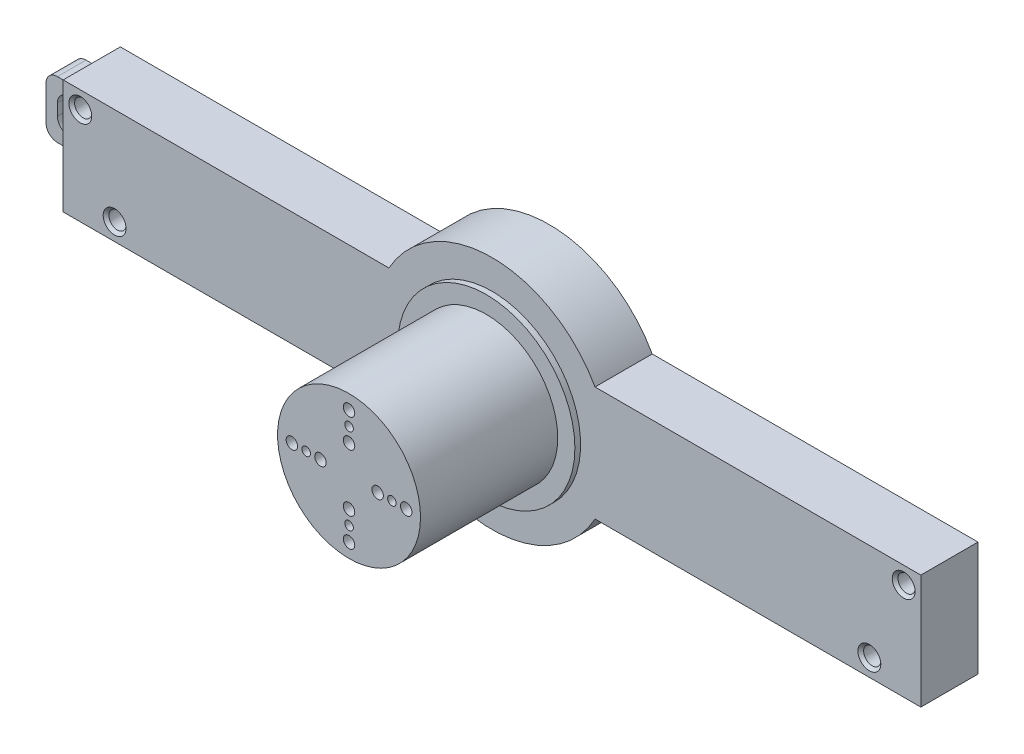
SolidWorks part; units mm, degrees
ref_plane "Płaszczyzna przednia" through (0, 0, 0) normal (0, 0, 1) x (1, 0, 0)
ref_plane "Płaszczyzna górna" through (0, 0, 0) normal (0, 1, 0) x (1, 0, 0)
ref_plane "Płaszczyzna prawa" through (0, 0, 0) normal (1, 0, 0) x (0, 0, -1)
sketch "Szkic1" plane through (0, 0, 0) normal (0, 0, 1) x (1, 0, 0)
  line L1 (-75, -10) -> (75, -10)
  line L2 (-75, -10) -> (-75, 10)
  line L3 (-75, 10) -> (75, 10)
  line L4 (75, -10) -> (75, 10)
  line L5 (-75, -10) -> (75, 10) construction
  line L6 (-75, 10) -> (75, -10) construction
  point P0 (0, 0)
  dimension "D1" = 150
  dimension "D2" = 20
extrude "Dodanie-wyciągnięcie1" add sketch "Szkic1" along normal blind 10
sketch "Szkic2" plane through (0, 0, 10) normal (0, 0, 1) x (1, 0, 0)
  circle A0 centre (0, 0) radius 20.6112
extrude "Dodanie-wyciągnięcie2" add sketch "Szkic2" against normal blind 10
sketch "Szkic3" plane through (0, 0, 10) normal (0, 0, 1) x (1, 0, 0)
  circle A0 centre (0, 0) radius 12.5
  dimension "D1" = 25
extrude "Dodanie-wyciągnięcie5" add sketch "Szkic3" along normal blind 25 contours A0
sketch "Szkic8" plane through (0, 0, 10) normal (0, 0, 1) x (1, 0, 0)
  circle A0 centre (0, 0) radius 15.5
  dimension "D1" = 31
extrude "Dodanie-wyciągnięcie6" add sketch "Szkic8" along normal blind 1
sketch "Szkic9" plane through (0, 0, 0) normal (0, 0, -1) x (-1, 0, 0)
  line L0 (-75, -10) -> (-75, 10) construction
  line L1 (-75, 10) -> (-18.0228, 10) construction
  line L2 (-18.0228, -10) -> (-75, -10) construction
  line L3 (0, 19.25) -> (0, -19.25) construction
  circle A0 centre (-72, 7) radius 1.5
  circle A1 centre (-66, -7) radius 1.5
  circle A2 centre (66, -7) radius 1.5
  circle A3 centre (72, 7) radius 1.5
  dimension "D1" = 3
  dimension "D2" = 3
  dimension "D3" = 3
  dimension "D4" = 3
  dimension "3" = 3
  dimension "9" = 9
extrude "Wytnij-wyciągnięcie1" cut sketch "Szkic9" against normal blind 10
chamfer "Sfazowanie1" distance 0.5 angle 45 4 edges at (-64.5, -7, 10) (-70.5, 7, 10) (64.5, -7, 10) (70.5, 7, 10)
sketch "Szkic10" plane through (-75, 0, 0) normal (-1, 0, 0) x (0, 0, 1)
  line L0 (0, 10) -> (0, -10) construction
  line L1 (5, -5) -> (0, -5)
  line L2 (5, -5) -> (5, 5)
  line L3 (5, 5) -> (0, 5)
  line L4 (0, -5) -> (0, 5)
  line L5 (5, -5) -> (0, 5) construction
  line L6 (5, 5) -> (0, -5) construction
  point P0 (2.5, 0)
  dimension "D1" = 10
  dimension "D2" = 5
extrude "Dodanie-wyciągnięcie7" add sketch "Szkic10" along normal blind 8
sketch "Szkic11" plane through (0, 0, 0) normal (0, 0, -1) x (-1, 0, 0)
  line L0 (75, 10) -> (75, -10) construction
  line L1 (75, -3) -> (81, -3)
  line L2 (75, -3) -> (75, 3)
  line L3 (75, 3) -> (81, 3)
  line L4 (81, -3) -> (81, 3)
  line L5 (75, -3) -> (81, 3) construction
  line L6 (75, 3) -> (81, -3) construction
  line L7 (83, -5) -> (75, -5) construction
  line L8 (83, 5) -> (83, -5) construction
  line L9 (83, 5) -> (75, 5) construction
  point P0 (78, 0)
  dimension "D1" = 0
  dimension "D2" = 2
  dimension "D3" = 2
  dimension "D4" = 2
extrude "Wytnij-wyciągnięcie2" cut sketch "Szkic11" against normal blind 8
fillet "Zaokrąglenie1" radius 2 4 edges at (-83, -5, 2.5) (-83, 5, 2.5) (-81, -3, 2.5) (-81, 3, 2.5)
sketch "Szkic12" plane through (0, 0, 35) normal (0, 0, 1) x (1, 0, 0)
  circle A0 centre (-5, 0) radius 1
  circle A1 centre (-10, 0) radius 1
  circle A2 centre (0, 10) radius 1
  circle A3 centre (0, 5) radius 1
  circle A4 centre (10, 0) radius 1
  circle A5 centre (5, 0) radius 1
  circle A6 centre (0, -10) radius 1
  circle A7 centre (0, -5) radius 1
  circle A8 centre (-7.5, 0) radius 0.75
  circle A9 centre (0, 7.5) radius 0.75
  circle A10 centre (7.5, 0) radius 0.75
  circle A11 centre (0, -7.5) radius 0.75
  point P20 (0, 0)
  point P29 (0, 0)
  dimension "D1" = 2
  dimension "D2" = 5
  dimension "D3" = 5
  dimension "D5" = 2.5
  dimension "D4" = 4
  dimension "D6" = 4
extrude "Wytnij-wyciągnięcie3" cut sketch "Szkic12" against normal blind 5
